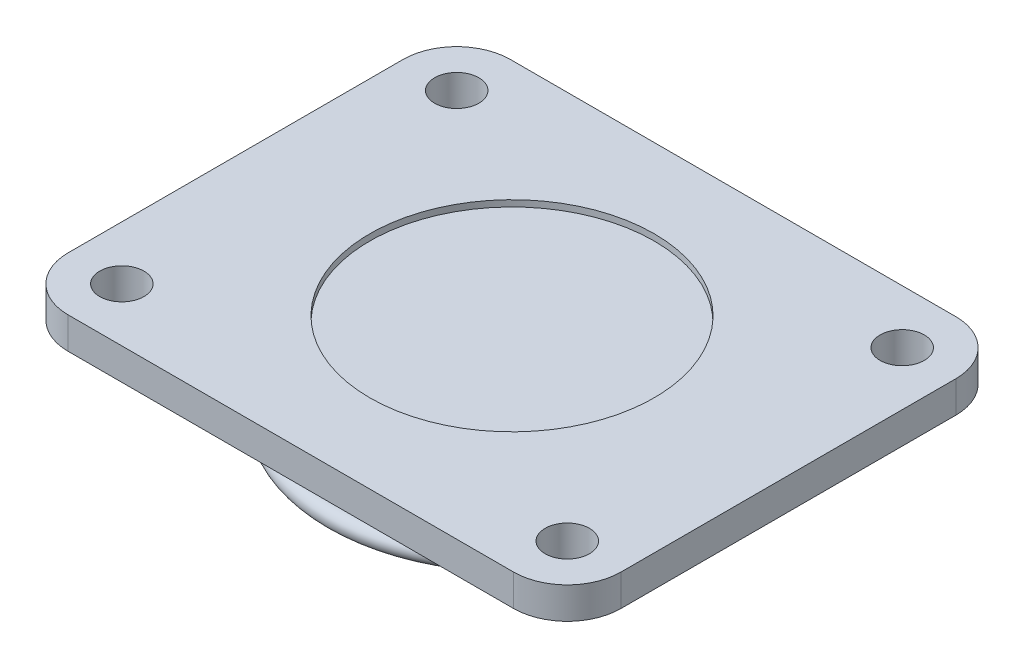
SolidWorks part; units mm, degrees
ref_plane "Front" through (0, 0, 0) normal (0, 0, 1) x (1, 0, 0)
ref_plane "Top" through (0, 0, 0) normal (0, 1, 0) x (1, 0, 0)
ref_plane "Right" through (0, 0, 0) normal (1, 0, 0) x (0, 0, -1)
sketch "Sketch1" plane through (0, 0, 0) normal (0, 1, 0) x (1, 0, 0)
  line L1 (-70.5, -70) -> (70.5, -70)
  line L2 (-87.5, -53) -> (-87.5, 53)
  line L3 (-70.5, 70) -> (70.5, 70)
  line L4 (87.5, -53) -> (87.5, 53)
  line L5 (-87.5, -70) -> (87.5, 70) construction
  line L6 (-87.5, 70) -> (87.5, -70) construction
  arc A0 (-70.5, -70) -> (-87.5, -53) centre (-70.5, -53) cw
  arc A1 (70.5, -70) -> (87.5, -53) centre (70.5, -53) ccw
  arc A2 (70.5, 70) -> (87.5, 53) centre (70.5, 53) cw
  arc A3 (-87.5, 53) -> (-70.5, 70) centre (-70.5, 53) cw
  circle A4 centre (70.5, -53) radius 7
  circle A5 centre (70.5, 53) radius 7
  circle A6 centre (-70.5, 53) radius 7
  circle A7 centre (-70.5, -53) radius 7
  point P0 (0, 0)
  dimension "D3" = 17
  dimension "D4" = 14
  dimension "D1" = 140
  dimension "D2" = 175
extrude "Boss-Extrude1" add sketch "Sketch1" along normal blind 10
sketch "Sketch2" plane through (0, 10, 0) normal (0, 1, 0) x (1, 0, 0)
  circle A0 centre (0, 0) radius 45
  dimension "D1" = 90
extrude "Cut-Extrude1" cut sketch "Sketch2" against normal blind 2
sketch "Sketch3" plane through (0, 0, 0) normal (0, -1, 0) x (1, 0, 0)
  circle A0 centre (0, 0) radius 56
  dimension "D1" = 112
extrude "Boss-Extrude2" add sketch "Sketch3" along normal blind 20
sketch "Sketch4" plane through (0, 0, 0) normal (1, 0, 0) x (0, 0, -1)
  line L0 (-56, 0) -> (-56, -20) construction
  line L1 (0, 0) -> (0, -32.4306) construction
  line L2 (-56, 0) -> (56, 0) construction
  circle A0 centre (-56, -17) radius 3
  dimension "D1" = 6
revolve "Revolve1" add sketch "Sketch4" angle 360 about L1
sketch "Sketch5" plane through (0, -20, 0) normal (0, -1, 0) x (1, 0, 0)
  circle A0 centre (0, 0) radius 7.5
  dimension "D1" = 15
extrude "Boss-Extrude3" add sketch "Sketch5" along normal blind 25
cosmetic thread "Cosmetic Thread1" parameters "D1"=5, "D2"=11.797
chamfer "Chamfer1" distance 1 angle 45 1 edges at (0, -45, -7.5)
